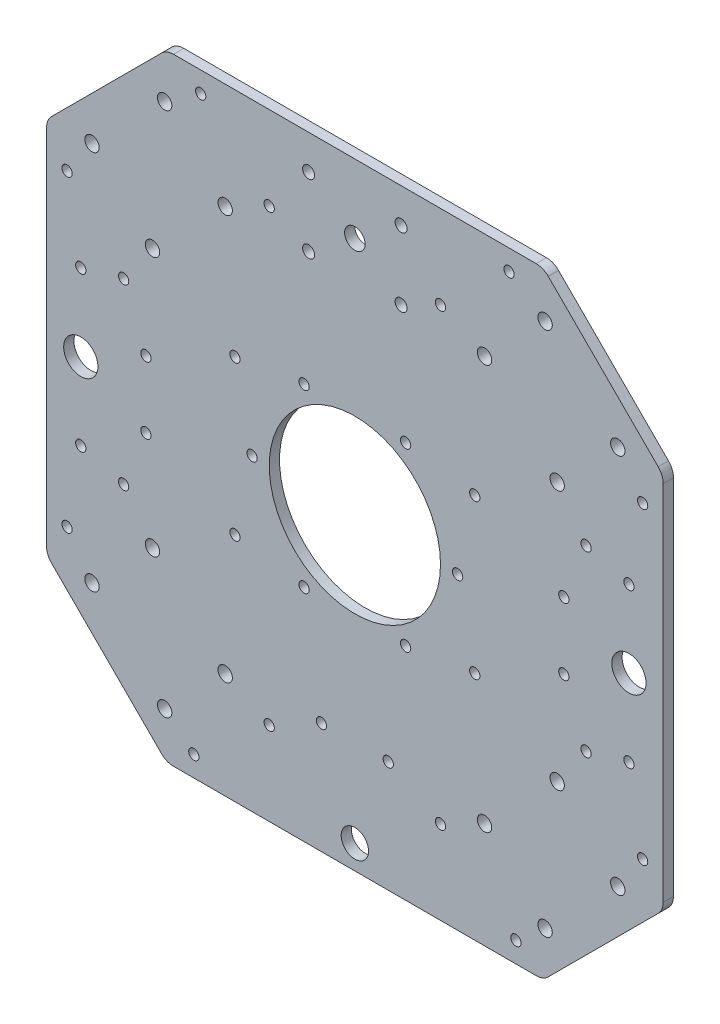
SolidWorks part; units mm, degrees
ref_plane "前视基准面" through (0, 0, 0) normal (0, 0, 1) x (1, 0, 0)
ref_plane "上视基准面" through (0, 0, 0) normal (0, 1, 0) x (1, 0, 0)
ref_plane "右视基准面" through (0, 0, 0) normal (1, 0, 0) x (0, 0, -1)
sketch "草图1" plane through (0, 0, 0) normal (0, 0, 1) x (1, 0, 0)
  line L0 (0, 90) -> (0, -90) construction
  line L1 (-90, 90) -> (90, 90)
  line L2 (-90, 90) -> (-90, -90)
  line L3 (-90, -90) -> (90, -90)
  line L4 (90, 90) -> (90, -90)
  line L5 (-90, 90) -> (90, -90) construction
  line L6 (-90, -90) -> (90, 90) construction
  line L7 (-90, 0) -> (90, 0) construction
  point P0 (0, 0)
  dimension "D1" = 180
  dimension "D2" = 180
extrude "凸台-拉伸1" add sketch "草图1" along normal blind 3
sketch "草图2" plane through (0, 0, 3) normal (0, 0, 1) x (1, 0, 0)
  line L0 (-90, 90) -> (90, -90) construction
  line L1 (-90, -90) -> (90, 90) construction
  line L7 (-90, 90) -> (-55, 90)
  line L8 (-90, 90) -> (90, 90) construction
  line L9 (-90, 90) -> (-90, 55)
  line L10 (-90, 90) -> (-90, -90) construction
  line L11 (-55, 90) -> (-90, 55)
  line L12 (90, 90) -> (55, 90)
  line L13 (55, 90) -> (90, 55)
  line L14 (90, 90) -> (90, -90) construction
  line L15 (90, 55) -> (90, 90)
  line L16 (-90, -90) -> (-90, -55)
  line L17 (-90, -55) -> (-55, -90)
  line L18 (-90, -90) -> (90, -90) construction
  line L19 (-55, -90) -> (-90, -90)
  line L20 (90, -90) -> (90, -55)
  line L21 (90, -55) -> (55, -90)
  line L22 (55, -90) -> (90, -90)
  point P11 (0, 0)
  point P12 (-90, 90)
  point P13 (2.8235, 105)
  point P15 (0, 0)
  dimension "D1" = 35
  dimension "D2" = 35
  dimension "D3" = 35
  dimension "D4" = 35
  dimension "D5" = 35
  dimension "D6" = 35
  dimension "D7" = 35
  dimension "D8" = 35
extrude "切除-拉伸1" cut sketch "草图2" against normal blind 3
sketch "草图3" plane through (0, 0, 3) normal (0, 0, 1) x (1, 0, 0)
  circle A0 centre (55.5294, 76.7426) radius 2.1
  circle A1 centre (76.7426, 55.5294) radius 2.1
  circle A2 centre (59.065, 37.8518) radius 2.1
  circle A3 centre (37.8518, 59.065) radius 2.1
  circle A4 centre (-55.5294, 76.7426) radius 2.1
  circle A5 centre (-37.8518, 59.065) radius 2.1
  circle A6 centre (-59.065, 37.8518) radius 2.1
  circle A7 centre (-76.7426, 55.5294) radius 2.1
  circle A8 centre (-59.065, -37.8518) radius 2.1
  circle A9 centre (-76.7426, -55.5294) radius 2.1
  circle A10 centre (-37.8518, -59.065) radius 2.1
  circle A11 centre (-55.5294, -76.7426) radius 2.1
  circle A12 centre (76.7426, -55.5294) radius 2.1
  circle A13 centre (55.5294, -76.7426) radius 2.1
  circle A14 centre (37.8518, -59.065) radius 2.1
  circle A15 centre (59.065, -37.8518) radius 2.1
extrude "切除-拉伸2" cut sketch "草图3" against normal blind 3
sketch "草图4" plane through (0, 0, 3) normal (0, 0, 1) x (1, 0, 0)
  circle A0 centre (0, 0) radius 25
  circle A1 centre (67.5, 26) radius 1.5
  circle A2 centre (67.5, -26) radius 1.5
  circle A5 centre (-67.5, -26) radius 1.5
  circle A6 centre (-67.5, 26) radius 1.5
  point P33 (0, 69.5)
  point P45 (69.5, 0)
  dimension "D1" = 50
extrude "切除-拉伸3" cut sketch "草图4" against normal blind 3
sketch "草图5" plane through (0, 0, 3) normal (0, 0, 1) x (1, 0, 0)
  line L0 (-25, 0) -> (-35, 0) construction
  line L1 (-90, 0) -> (90, 0) construction
  line L2 (-35, 22.5) -> (-35, -22.5) construction
  line L3 (-35, 22.5) -> (-80, 22.5) construction
  line L4 (-80, 22.5) -> (-80, -22.5) construction
  line L5 (-80, -22.5) -> (-35, -22.5) construction
  line L6 (25, 0) -> (35, 0) construction
  line L7 (35, 22.5) -> (35, -22.5) construction
  line L8 (35, 22.5) -> (80, 22.5) construction
  line L9 (80, 22.5) -> (80, -22.5) construction
  line L10 (80, -22.5) -> (35, -22.5) construction
  line L11 (-35, 0) -> (-61, 0) construction
  line L12 (-90, 0) -> (-80, 0) construction
  line L13 (35, 0) -> (61, 0) construction
  line L14 (61, 9.75) -> (61, -9.75) construction
  line L15 (-90, 55) -> (-90, -55) construction
  line L23 (-61, 9.75) -> (-61, -9.75) construction
  circle A0 centre (0, 0) radius 25 construction
  circle A11 centre (61, 9.75) radius 1.5
  circle A12 centre (61, -9.75) radius 1.5
  circle A13 centre (80, 0) radius 5
  circle A15 centre (35, 22.5) radius 1.5
  circle A16 centre (35, -22.5) radius 1.5
  circle A17 centre (80, -22.5) radius 1.5
  circle A18 centre (80, 22.5) radius 1.5
  circle A26 centre (-80, 22.5) radius 1.5
  circle A27 centre (-80, -22.5) radius 1.5
  circle A28 centre (-35, -22.5) radius 1.5
  circle A29 centre (-35, 22.5) radius 1.5
  circle A30 centre (-61, 9.75) radius 1.5
  circle A31 centre (-61, -9.75) radius 1.5
  circle A32 centre (-80, 0) radius 5
  point P9 (-35, 0)
  point P20 (35, 0)
  point P29 (-61, 0)
  point P31 (0, 35)
  point P36 (61, 0)
  point P49 (9, 61)
  point P62 (-61, 0)
  dimension "D4" = 3
  dimension "D10" = 10
  dimension "D13" = 10
  dimension "D23" = 3
  dimension "D24" = 3
  dimension "D1" = 10
  dimension "D2" = 45
  dimension "D3" = 45
  dimension "D5" = 10
  dimension "D6" = 45
  dimension "D7" = 45
  dimension "D8" = 26
  dimension "D9" = 10
  dimension "D11" = 26
  dimension "D12" = 19.5
  dimension "D22" = 19.5
extrude "切除-拉伸4" cut sketch "草图5" against normal blind 3
sketch "草图6" plane through (0, 0, 3) normal (0, 0, 1) x (1, 0, 0)
  circle A0 centre (14.8205, 25.6699) radius 1.5
  circle A1 centre (-14.8205, 25.6699) radius 1.5
  circle A2 centre (-30, 0) radius 1.5
  circle A3 centre (-14.8205, -25.6699) radius 1.5
  circle A4 centre (14.8205, -25.6699) radius 1.5
  circle A5 centre (30, 0) radius 1.5
extrude "切除-拉伸5" cut sketch "草图6" against normal blind 3
fillet "圆角2" radius 5 8 edges at (55, -90, 1.5) (90, -55, 1.5) (90, 55, 1.5) (55, 90, 1.5) (-55, 90, 1.5) (-90, 55, 1.5) (-90, -55, 1.5) (-55, -90, 1.5)
sketch "草图7" plane through (0, 0, 3) normal (0, 0, 1) x (1, 0, 0)
  line L0 (0, 0) -> (0, 65.6) construction
  line L2 (-25, 65.6) -> (25, 65.6) construction
  circle A0 centre (-25, 65.6) radius 1.5
  circle A1 centre (25, 65.6) radius 1.5
  point P8 (0, 65.6)
  dimension "D2" = 3
  dimension "D3" = 3
  dimension "D1" = 50
extrude "切除-拉伸6" cut sketch "草图7" against normal blind 3
sketch "草图8" plane through (0, 0, 3) normal (0, 0, 1) x (1, 0, 0)
  line L0 (0, 0) -> (0, -65.6) construction
  line L2 (25, -65.6) -> (-25, -65.6) construction
  circle A0 centre (25, -65.6) radius 1.5
  circle A1 centre (-25, -65.6) radius 1.5
  point P8 (0, -65.6)
  dimension "D2" = 3
  dimension "D3" = 3
  dimension "D1" = 50
extrude "切除-拉伸7" cut sketch "草图8" against normal blind 3
sketch "草图10" plane through (0, 0, 3) normal (0, 0, 1) x (1, 0, 0)
  line L0 (0, 90) -> (0, 84) construction
  line L1 (-52.9289, -90) -> (52.9289, -90) construction
  line L2 (0, 90) -> (0, -90) construction
  line L3 (-90, 0) -> (90, 0) construction
  line L4 (90, -52.9289) -> (90, 52.9289) construction
  line L5 (-47, -84) -> (47, -84) construction
  line L6 (-84, 45) -> (-84, -45) construction
  line L7 (-90, 52.9289) -> (-90, -52.9289) construction
  line L8 (90, 0) -> (84, 0) construction
  line L10 (84, 45) -> (84, -45) construction
  line L11 (-45, 84) -> (45, 84) construction
  circle A0 centre (-47, -84) radius 1.5
  circle A1 centre (47, -84) radius 1.5
  circle A4 centre (-84, -45) radius 1.5
  circle A5 centre (-84, 45) radius 1.5
  circle A8 centre (84, -45) radius 1.5
  circle A9 centre (84, 45) radius 1.5
  circle A10 centre (-45, 84) radius 1.5
  circle A11 centre (45, 84) radius 1.5
  point P8 (0, 0)
  point P14 (0, 0)
  point P17 (0, -84)
  point P20 (0, 84)
  point P21 (0, 84)
  point P25 (-84, 0)
  point P26 (-84, 0)
  point P33 (84, 0)
  point P34 (84, 0)
  point P37 (84, 0)
  dimension "D2" = 3
  dimension "D10" = 3
  dimension "D11" = 3
  dimension "D12" = 3
  dimension "D13" = 3
  dimension "D1" = 94
  dimension "D3" = 6
  dimension "D4" = 6
  dimension "D5" = 90
  dimension "D6" = 6
  dimension "D7" = 90
  dimension "D8" = 90
  dimension "D9" = 6
extrude "切除-拉伸9" cut sketch "草图10" against normal blind 3
sketch "草图11" plane through (0, 0, 3) normal (0, 0, 1) x (1, 0, 0)
  line L0 (0, -90) -> (0, -25) construction
  line L1 (-52.9289, -90) -> (52.9289, -90) construction
  line L2 (-9.75, -57.5) -> (9.75, -57.5) construction
  circle A0 centre (0, 0) radius 25 construction
  circle A1 centre (9.75, -57.5) radius 1.5
  circle A2 centre (-9.75, -57.5) radius 1.5
  circle A3 centre (0, -83) radius 4
  point P10 (0, -57.5)
  dimension "D2" = 3
  dimension "D3" = 8
  dimension "D1" = 19.5
extrude "切除-拉伸10" cut sketch "草图11" against normal blind 3
sketch "草图12" plane through (0, 0, 3) normal (0, 0, 1) x (1, 0, 0)
  line L0 (-45, 84) -> (45, 84) construction
  line L1 (0, 84) -> (0, 69.9) construction
  circle A0 centre (0, 69.9) radius 3
  dimension "D1" = 6
extrude "切除-拉伸11" cut sketch "草图12" against normal blind 3
sketch "草图13" plane through (0, 0, 3) normal (0, 0, 1) x (1, 0, 0)
  circle A0 centre (-13.5, 79.9409) radius 1.75
  circle A1 centre (-13.5, 59.8591) radius 1.75
  circle A2 centre (13.5, 59.8591) radius 1.75
  circle A3 centre (13.5, 79.9409) radius 1.75
extrude "切除-拉伸12" cut sketch "草图13" against normal blind 3
